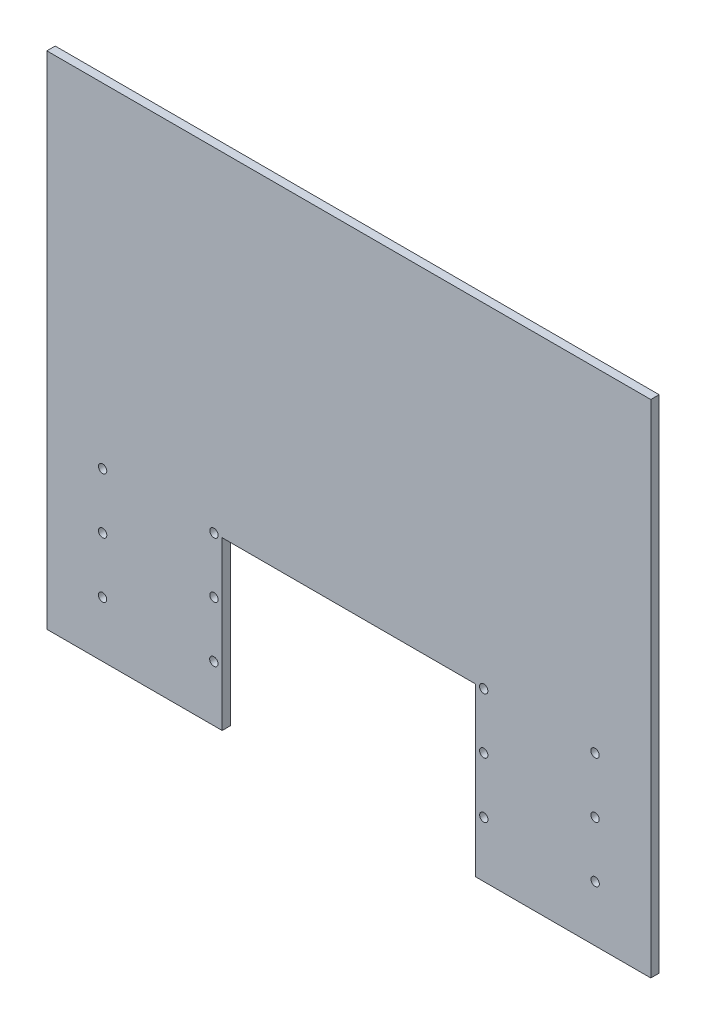
SolidWorks part; units mm, degrees
ref_plane "前视基准面" through (0, 0, 0) normal (0, 0, 1) x (1, 0, 0)
ref_plane "上视基准面" through (0, 0, 0) normal (0, 1, 0) x (1, 0, 0)
ref_plane "右视基准面" through (0, 0, 0) normal (1, 0, 0) x (0, 0, -1)
sketch "草图1" plane through (0, 0, 0) normal (0, 0, 1) x (1, 0, 0)
  line L0 (22.567, -52.4302) -> (22.567, -22.4302)
  line L1 (-54.433, 37.5698) -> (54.067, 37.5698)
  line L2 (-54.433, 37.5698) -> (-54.433, -52.4302)
  line L3 (-54.433, -52.4302) -> (-22.933, -52.4302)
  line L4 (-0.183, 37.5698) -> (-0.183, -22.4302)
  line L7 (22.567, -22.4302) -> (-22.933, -22.4302)
  line L8 (-22.933, -52.4302) -> (-22.933, -22.4302)
  line L9 (54.067, -52.4302) -> (22.567, -52.4302)
  line L10 (54.067, 37.5698) -> (54.067, -52.4302)
  line L11 (-24.4133, -32.4302) -> (-0.933, -32.4302)
  circle A0 centre (-44.4133, -22.4302) radius 0.75
  circle A1 centre (-24.4133, -22.4302) radius 0.75
  circle A2 centre (-24.433, -42.4302) radius 0.75
  circle A3 centre (-24.4133, -32.4302) radius 0.75
  circle A4 centre (-44.4133, -32.4302) radius 0.75
  circle A5 centre (-44.433, -42.4302) radius 0.75
  circle A6 centre (24.067, -42.4302) radius 0.75
  circle A7 centre (44.067, -42.4302) radius 0.75
  circle A8 centre (44.0473, -32.4302) radius 0.75
  circle A9 centre (24.0473, -32.4302) radius 0.75
  circle A10 centre (24.0473, -22.4302) radius 0.75
  circle A11 centre (44.0473, -22.4302) radius 0.75
  point P16 (-55.9486, 17.5599)
  point P25 (-74.0904, 22.4368)
  dimension "D3" = 10
  dimension "D4" = 1.5
  dimension "D5" = 1.5
  dimension "D6" = 10
  dimension "D7" = 10
  dimension "D8" = 10
  dimension "D9" = 20
  dimension "D10" = 10
  dimension "D11" = 20
  dimension "D12" = 10
  dimension "D13" = 10
  dimension "D14" = 20
  dimension "D2" = 90
  dimension "D15" = 22.75
  dimension "D16" = 30
extrude "凸台-拉伸2" add sketch "草图1" along normal blind 1.5 contours L3 L8 L7 L4 L1 L2 A5 A4 A3 A2 A1 A0 | L10 L1 L4 L7 L0 L9 A10 A8 A6 A7 A9 A11
